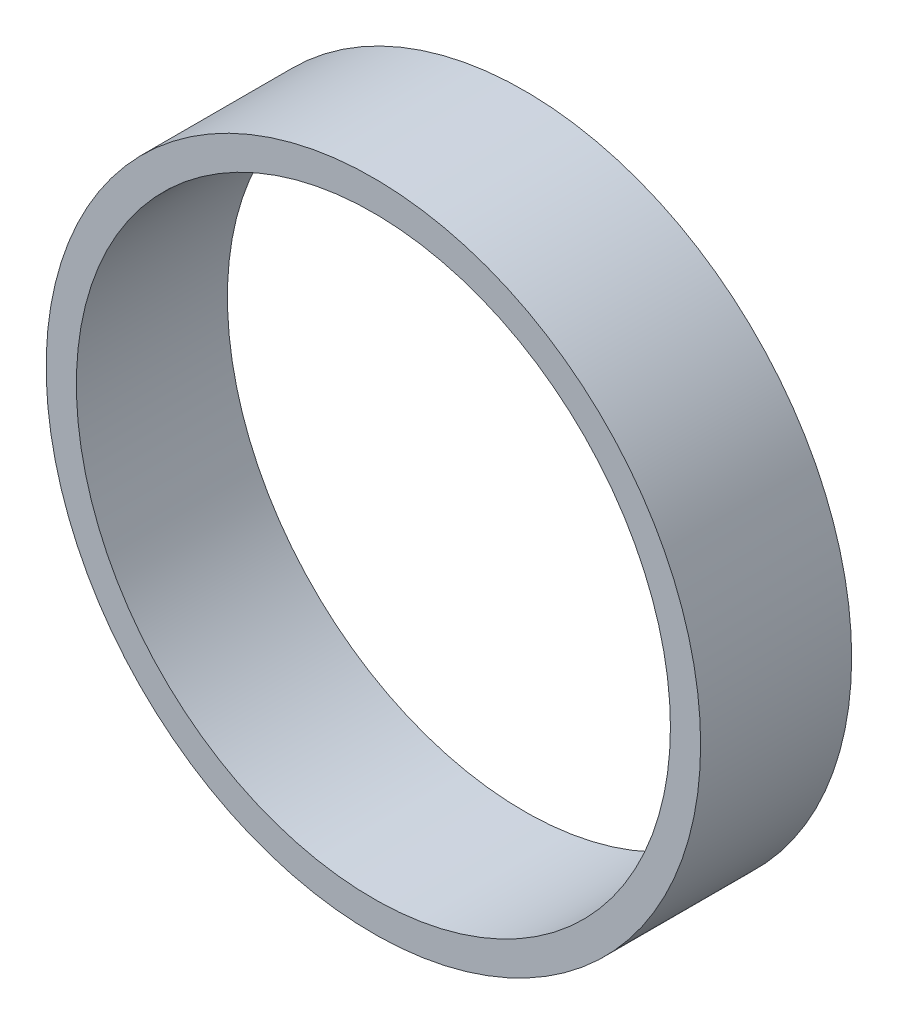
SolidWorks part; units mm, degrees
ref_plane "Plan de face" through (0, 0, 0) normal (0, 0, 1) x (1, 0, 0)
ref_plane "Plan de dessus" through (0, 0, 0) normal (0, 1, 0) x (1, 0, 0)
ref_plane "Plan de droite" through (0, 0, 0) normal (1, 0, 0) x (0, 0, -1)
sketch "Esquisse1" plane through (0, 0, 0) normal (0, 0, 1) x (1, 0, 0)
  circle A0 centre (0, 0) radius 32.5
  circle A1 centre (0, 0) radius 29.5
extrude "Boss.-Extru.1" add sketch "Esquisse1" along normal blind 15
